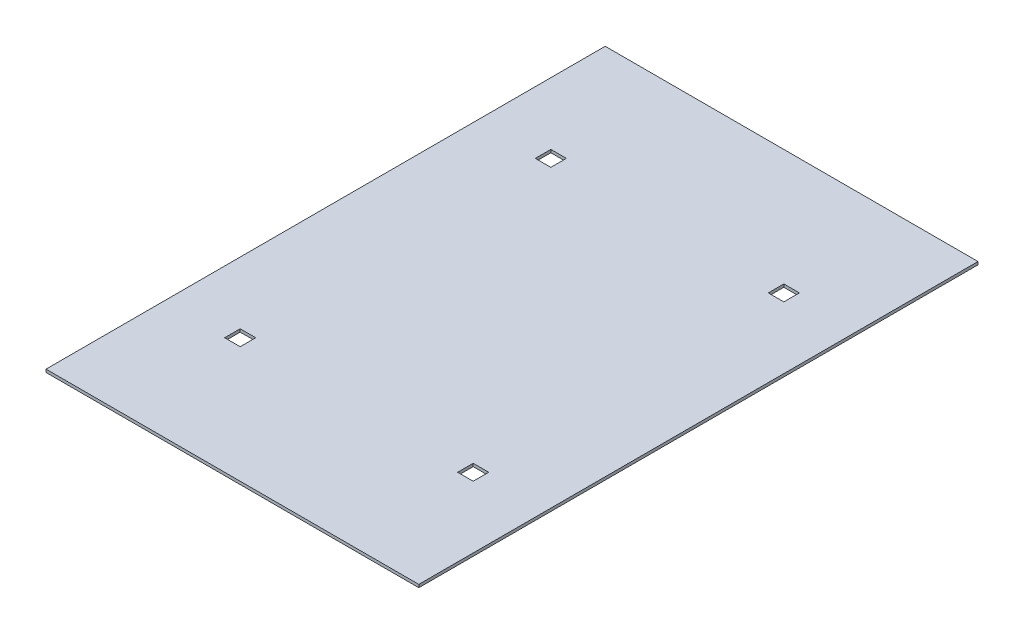
SolidWorks part; units mm, degrees
ref_plane "Front Plane" through (0, 0, 0) normal (0, 0, 1) x (1, 0, 0)
ref_plane "Top Plane" through (0, 0, 0) normal (0, 1, 0) x (1, 0, 0)
ref_plane "Right Plane" through (0, 0, 0) normal (1, 0, 0) x (0, 0, -1)
sketch "Sketch1" plane through (0, 0, 0) normal (0, 1, 0) x (1, 0, 0)
  line L1 (0, 0) -> (609.6, 0)
  line L2 (0, 0) -> (0, 914.4)
  line L3 (0, 914.4) -> (609.6, 914.4)
  line L4 (609.6, 0) -> (609.6, 914.4)
  dimension "D1" = 609.6
  dimension "D2" = 914.4
extrude "Boss-Extrude1" add sketch "Sketch1" along normal blind 4.7625
sketch "Sketch2" plane through (0, 4.7625, 0) normal (0, 1, 0) x (1, 0, 0)
  line L0 (0, 914.4) -> (0, 0) construction
  line L1 (101.6, 723.9) -> (127, 723.9)
  line L2 (101.6, 723.9) -> (101.6, 698.5)
  line L3 (101.6, 698.5) -> (127, 698.5)
  line L4 (127, 723.9) -> (127, 698.5)
  line L5 (482.6, 723.9) -> (508, 723.9)
  line L6 (482.6, 723.9) -> (482.6, 698.5)
  line L7 (482.6, 698.5) -> (508, 698.5)
  line L8 (508, 723.9) -> (508, 698.5)
  line L9 (101.6, 215.9) -> (127, 215.9)
  line L10 (101.6, 215.9) -> (101.6, 190.5)
  line L11 (101.6, 190.5) -> (127, 190.5)
  line L12 (127, 215.9) -> (127, 190.5)
  line L13 (508, 190.5) -> (482.6, 190.5)
  line L14 (508, 190.5) -> (508, 215.9)
  line L15 (508, 215.9) -> (482.6, 215.9)
  line L16 (482.6, 190.5) -> (482.6, 215.9)
  line L17 (609.6, 0) -> (609.6, 914.4) construction
  line L18 (609.6, 914.4) -> (0, 914.4) construction
  line L19 (0, 0) -> (609.6, 0) construction
  dimension "D1" = 25.4
  dimension "D2" = 101.6
  dimension "D3" = 101.6
  dimension "D4" = 190.5
  dimension "D5" = 190.5
extrude "Cut-Extrude1" cut sketch "Sketch2" against normal through all
